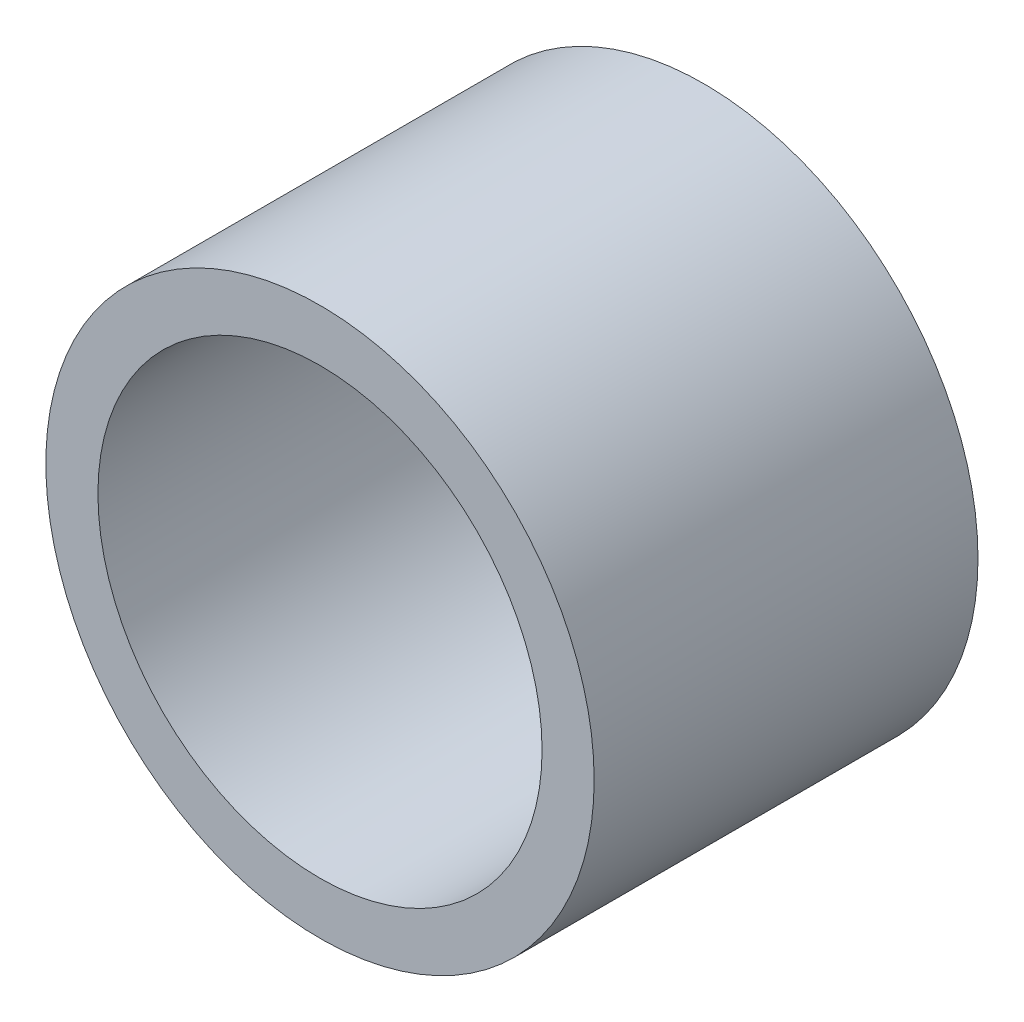
SolidWorks part; units mm, degrees
ref_plane "Front Plane" through (0, 0, 0) normal (0, 0, 1) x (1, 0, 0)
ref_plane "Top Plane" through (0, 0, 0) normal (0, 1, 0) x (1, 0, 0)
ref_plane "Right Plane" through (0, 0, 0) normal (1, 0, 0) x (0, 0, -1)
sketch "Sketch1" plane through (0, 0, 0) normal (0, 0, 1) x (1, 0, 0)
  circle A0 centre (0, 0) radius 4.05
  circle A1 centre (0, 0) radius 5
extrude "Boss-Extrude1" add sketch "Sketch1" along normal blind 7
